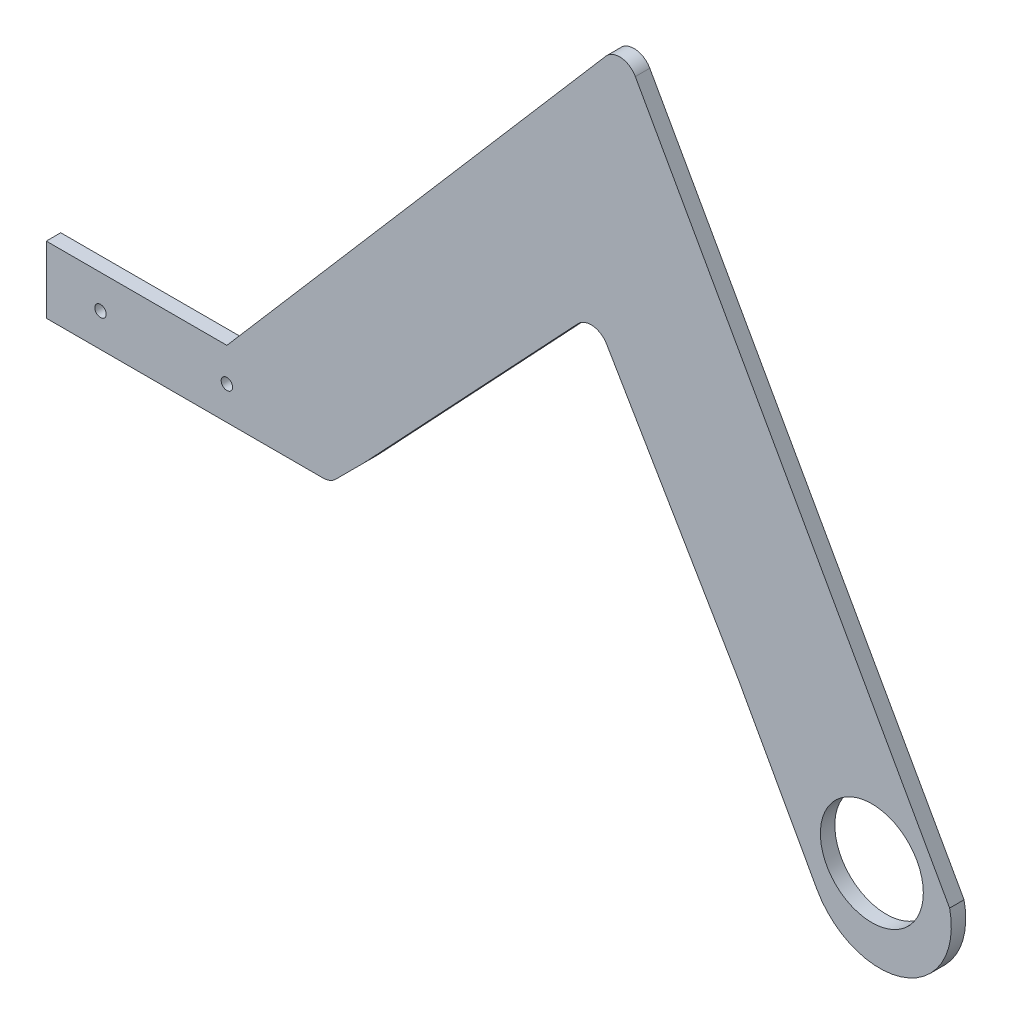
SolidWorks part; units mm, degrees
ref_plane "Alzado" through (0, 0, 0) normal (0, 0, 1) x (1, 0, 0)
ref_plane "Planta" through (0, 0, 0) normal (0, 1, 0) x (1, 0, 0)
ref_plane "Vista lateral" through (0, 0, 0) normal (1, 0, 0) x (0, 0, -1)
sketch "Croquis1" plane through (0, 0, 0) normal (0, 0, 1) x (1, 0, 0)
  line L0 (0, 0) -> (-35, 0) construction
  line L1 (0, 0) -> (178.55, 0) construction
  line L2 (178.55, 0) -> (178.55, -25.63) construction
  line L3 (109.59, 0) -> (109.59, 136.47) construction
  line L4 (101.74, 0) -> (101.74, 67.88) construction
  line L5 (37.91, 0) -> (97.1655, 63.0152)
  line L6 (105.1201, 62.1209) -> (141.58, 0)
  line L7 (0, -9.25) -> (0, 9.25) construction
  line L8 (0, 9.25) -> (104.9221, 131.0512)
  line L9 (-35, -9.25) -> (-35, 9.25) construction
  line L10 (0, 9.25) -> (-35, 9.25)
  line L11 (-35, -9.25) -> (0, -9.25)
  line L12 (37.91, 0) -> (37.91, -23.3636) construction
  line L13 (37.91, 0) -> (30.1245, -7.7855)
  line L14 (37.91, -4.25) -> (37.91, 0)
  line L15 (-35, 0) -> (-50, 0) construction
  line L16 (-50, -9.25) -> (-50, 9.25)
  line L17 (-50, 9.25) -> (-35, 9.25)
  line L18 (-50, -9.25) -> (-35, -9.25)
  line L19 (26.5889, -9.25) -> (0, -9.25)
  line L20 (113.0762, 130.225) -> (200.08, -25.63)
  line L21 (141.58, 0) -> (155.71, -25.63)
  line L22 (153.7995, -22.1646) -> (163.3523, -39.4921) construction
  line L23 (153.7995, -22.1646) -> (163.3523, -39.4921)
  line L24 (37.91, 0) -> (30.1245, -7.7855)
  circle A0 centre (-35, 0) radius 1.58
  circle A1 centre (0, 0) radius 1.58
  circle A2 centre (178.55, -25.63) radius 14.25
  arc A3 (105.1201, 62.1209) -> (97.1655, 63.0152) centre (100.808, 59.59) ccw
  arc A4 (30.1245, -7.7855) -> (26.5889, -9.25) centre (26.5889, -4.25) cw
  arc A5 (163.3523, -39.4921) -> (200.08, -25.63) centre (180.7185, -29.9179) ccw
  arc A6 (113.0762, 130.225) -> (104.9221, 131.0512) centre (108.7104, 127.7879) ccw
  point P12 (141.58, 0)
  point P13 (37.91, 0)
  point P24 (-35, 0)
  point P28 (37.91, -9.25)
  point P33 (-50, 0)
  point P34 (155.71, -25.63)
  point P35 (178.55, -48.8)
  point P36 (200.08, -25.63)
  point P41 (162.8264, -38.5383)
  dimension "D2" = 3.16
  dimension "D5" = 28.5
  dimension "D12" = 5
  dimension "D14" = 5
  dimension "D20" = 5
  dimension "D1" = 35
  dimension "D3" = 178.55
  dimension "D4" = 25.63
  dimension "D6" = 109.59
  dimension "D7" = 136.47
  dimension "D8" = 7.85
  dimension "D9" = 67.88
  dimension "D10" = 31.99
  dimension "D11" = 63.83
  dimension "D13" = 9.25
  dimension "D15" = 15
  dimension "D16" = 21.53
  dimension "D17" = 23.17
  dimension "D18" = 22.84
  dimension "D19" = 14.74
extrude "Saliente-Extruir1" add sketch "Croquis1" along normal blind 4 contours L20 A6 L8 L10 L17 L16 L18 L11 L19 A4 L13 L5 A3 L6 L21 L23 A5 A0 A1 A2
